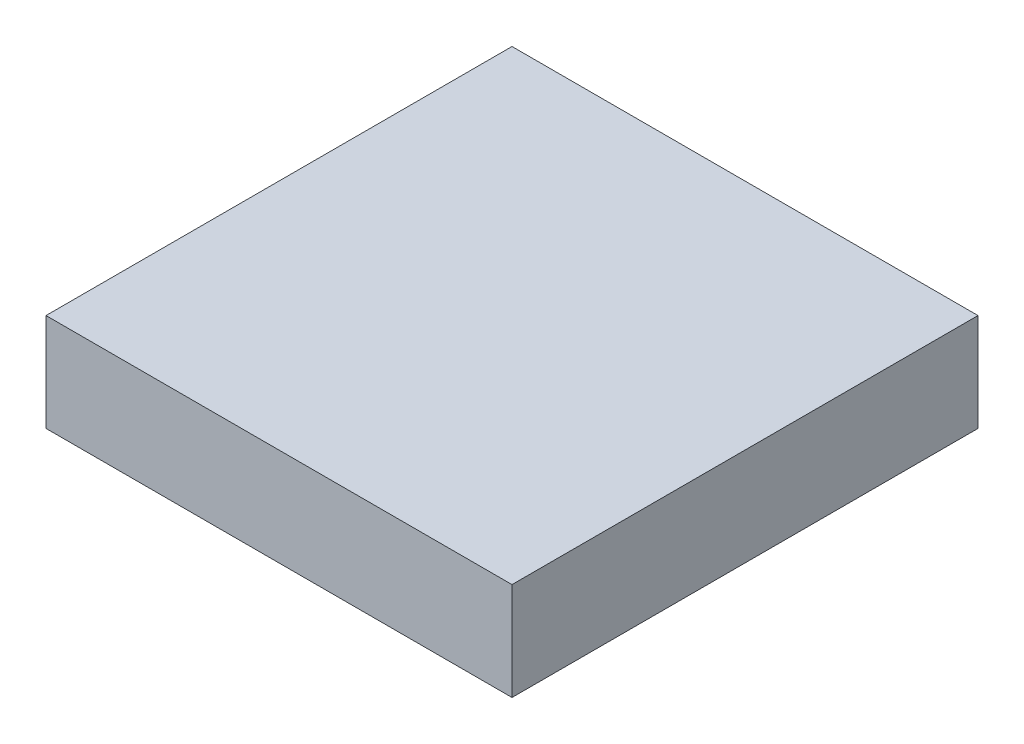
SolidWorks part; units mm, degrees
ref_plane "Front Plane" through (0, 0, 0) normal (0, 0, 1) x (1, 0, 0)
ref_plane "Top Plane" through (0, 0, 0) normal (0, 1, 0) x (1, 0, 0)
ref_plane "Right Plane" through (0, 0, 0) normal (1, 0, 0) x (0, 0, -1)
sketch "Sketch1" plane through (0, 0, 0) normal (0, 1, 0) x (1, 0, 0)
  line L1 (0, 0) -> (170.18, 0)
  line L2 (0, 0) -> (0, 170.18)
  line L3 (0, 170.18) -> (170.18, 170.18)
  line L4 (170.18, 0) -> (170.18, 170.18)
  dimension "D1" = 170.18
  dimension "D2" = 170.18
extrude "Boss-Extrude1" add sketch "Sketch1" along normal blind 35.7124
